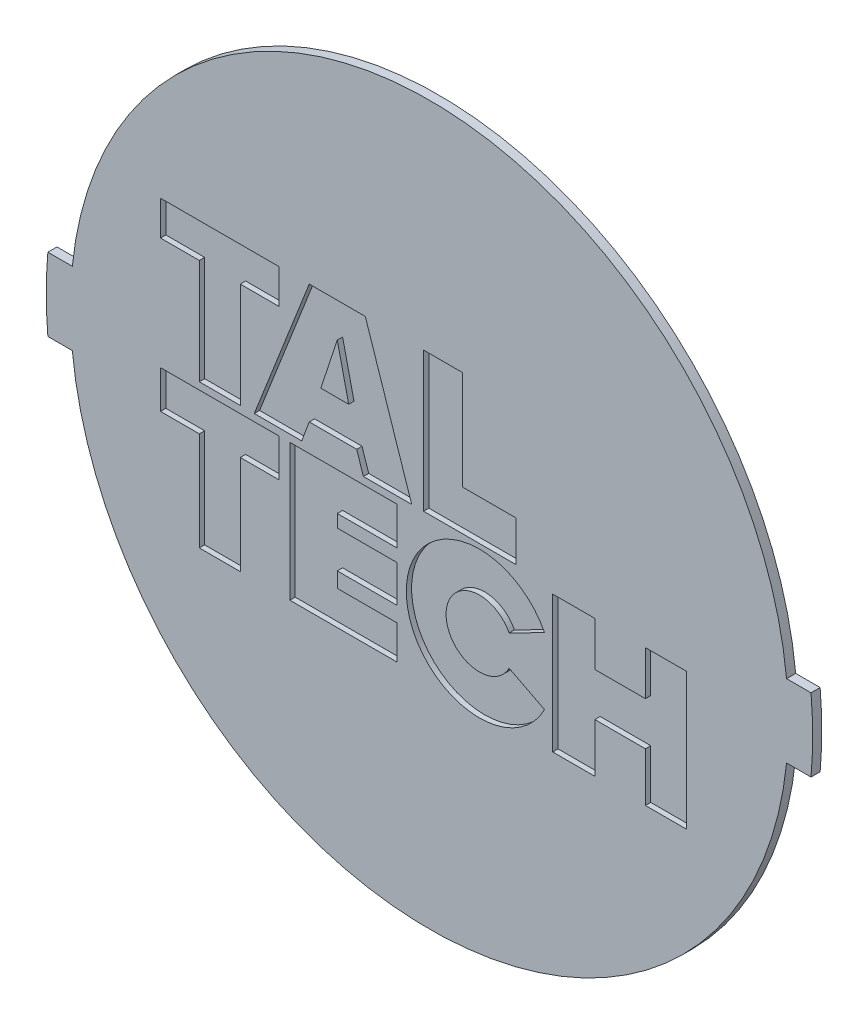
SolidWorks part; units mm, degrees
ref_plane "Alzado" through (0, 0, 0) normal (0, 0, 1) x (1, 0, 0)
ref_plane "Planta" through (0, 0, 0) normal (0, 1, 0) x (1, 0, 0)
ref_plane "Vista lateral" through (0, 0, 0) normal (1, 0, 0) x (0, 0, -1)
sketch "Croquis1" plane through (0, 0, 0) normal (0, 0, 1) x (1, 0, 0)
  circle A0 centre (0, 0) radius 59
  dimension "D1" = 118
extrude "Saliente-Extruir1" add sketch "Croquis1" along normal blind 1.5
sketch "Croquis2" plane through (0, 0, 1.5) normal (0, 0, 1) x (1, 0, 0)
  line L0 (-62.7136, 6) -> (62.7136, 6)
  line L1 (-62.7136, -6) -> (62.7136, -6)
  line L2 (55, 0) -> (-55, 0) construction
  arc A0 (-62.7136, 6) -> (-62.7136, -6) centre (0, 0) ccw
  arc A1 (62.7136, -6) -> (62.7136, 6) centre (0, 0) ccw
  dimension "D1" = 126
  dimension "D2" = 6
  dimension "D3" = 6
extrude "Saliente-Extruir2" add sketch "Croquis2" against normal blind 1.5
scale "Escala1" scale about centroid uniform scaling yes scale factor 0.8
sketch "Croquis7" plane through (0, 0, 1.35) normal (0, 0, 1) x (1, 0, 0)
  line L0 (0.66, 0) -> (-0.66, 0) construction
  line L1 (-35.3595, 18.3529) -> (-19.7701, 18.3529)
  line L2 (-35.3595, 18.3529) -> (-35.3595, 13.8178)
  line L3 (-18.3487, -18.9198) -> (-4.2815, -18.9198)
  line L4 (33.8005, -0.9414) -> (33.8005, -18.9198)
  line L5 (-35.3595, 18.3529) -> (-19.7701, 18.3529)
  line L6 (-35.3595, 18.3529) -> (-35.3595, 13.8178)
  line L7 (-30.2575, 0) -> (-24.8721, 0)
  line L8 (11.4086, 5.3146) -> (11.4086, 0)
  line L9 (-23.0297, 0) -> (-16.794, 0)
  line L10 (-35.3595, 18.3529) -> (-19.7701, 18.3529)
  line L11 (-35.3595, 18.3529) -> (-35.3595, 13.8178)
  line L12 (-35.3595, 13.8178) -> (-30.2575, 13.8178)
  line L13 (-19.7701, 18.3529) -> (-19.7701, 13.8178)
  line L14 (-30.2575, 0) -> (-24.8721, 0)
  line L15 (-30.2575, 0) -> (-30.2575, 13.8178)
  line L17 (-24.8721, 0) -> (-24.8721, 13.8178)
  line L18 (-0.7795, 18.3529) -> (4.3225, 18.3529)
  line L19 (-0.7795, 18.3529) -> (-0.7795, 5.3146)
  line L21 (4.3225, 18.3529) -> (4.3225, 5.3146)
  line L22 (11.4086, 0) -> (-0.7795, 0)
  line L23 (11.4086, 0) -> (11.4086, 5.3146)
  line L24 (11.4086, 5.3146) -> (4.3225, 5.3146)
  line L25 (-0.7795, 0) -> (-0.7795, 5.3146)
  line L26 (-16.794, 0) -> (-15.8019, 2.6573)
  line L27 (-15.8019, 2.6573) -> (-9.5662, 2.6573)
  line L28 (-9.5662, 2.6573) -> (-8.6842, 0)
  line L29 (-8.6842, 0) -> (-2.3384, 0)
  line L30 (-2.3384, 0) -> (-8.4298, 18.3529)
  line L31 (-8.4298, 18.3529) -> (-15.8019, 18.3529)
  line L32 (-15.8019, 18.3529) -> (-23.0297, 0)
  line L33 (-24.8721, 13.8178) -> (-19.7701, 13.8178)
  line L37 (10.4772, -8.2452) -> (15.1331, -5.8593)
  line L38 (-35.3595, -0.9414) -> (-19.7701, -0.9414)
  line L39 (-35.3595, -0.9414) -> (-35.3595, -5.9259)
  line L40 (-35.3595, -5.9259) -> (-30.2575, -5.9259)
  line L41 (-19.7701, -0.9414) -> (-19.7701, -5.9259)
  line L42 (-30.2575, -18.9198) -> (-24.8721, -18.9198)
  line L43 (-30.2575, -18.9198) -> (-30.2575, -5.9259)
  line L45 (-24.8721, -18.9198) -> (-24.8721, -5.9259)
  line L46 (-18.3487, -0.9414) -> (-4.2815, -0.9414)
  line L47 (-18.3487, -0.9414) -> (-18.3487, -18.9198)
  line L48 (-18.3487, -18.9198) -> (-4.2815, -18.9198)
  line L49 (-4.2815, -0.9414) -> (-4.2815, -5.9259)
  line L50 (-12.1159, -12.461) -> (-4.2815, -12.461)
  line L51 (-12.1159, -12.461) -> (-12.1159, -14.4548)
  line L52 (-12.1159, -14.4548) -> (-4.2815, -14.4548)
  line L54 (-12.1159, -5.9259) -> (-4.2815, -5.9259)
  line L55 (-12.1159, -5.9259) -> (-12.1159, -7.5874)
  line L56 (-12.1159, -7.5874) -> (-4.2815, -7.5874)
  line L58 (16.2101, -0.9414) -> (21.7483, -0.9414)
  line L59 (16.2101, -0.9414) -> (16.2101, -18.9198)
  line L60 (16.2101, -18.9198) -> (21.7483, -18.9198)
  line L61 (33.8005, -0.9414) -> (33.8005, -18.9198)
  line L62 (21.7483, -6.7566) -> (28.3942, -6.7566)
  line L63 (21.7483, -6.7566) -> (21.7483, -0.9414)
  line L65 (28.3942, -6.7566) -> (28.3942, -0.9414)
  line L66 (21.7483, -12.461) -> (28.3942, -12.461)
  line L67 (21.7483, -12.461) -> (21.7483, -18.9198)
  line L69 (28.3942, -12.461) -> (28.3942, -18.9198)
  line L70 (15.1331, -5.8593) -> (10.4772, -8.2452)
  line L71 (10.4772, -12.2462) -> (15.1331, -14.6322)
  line L72 (-24.8721, -5.9259) -> (-19.7701, -5.9259)
  line L73 (-4.2815, -7.5874) -> (-4.2815, -12.461)
  line L74 (-4.2815, -14.4548) -> (-4.2815, -18.9198)
  line L75 (28.3942, -0.9414) -> (33.8005, -0.9414)
  line L76 (28.3942, -18.9198) -> (33.8005, -18.9198)
  line L77 (28.3942, -18.9198) -> (33.8005, -18.9198)
  line L78 (16.2101, -18.9198) -> (21.7483, -18.9198)
  line L79 (-35.3595, -0.9414) -> (-35.3595, -5.9259)
  line L80 (-15.8019, 18.3529) -> (-8.4298, 18.3529)
  line L81 (-15.8019, 18.3529) -> (-8.4298, 18.3529)
  line L82 (-23.0297, 0) -> (-16.794, 0)
  line L83 (-8.6842, 0) -> (-2.3384, 0)
  line L84 (-0.7795, 0) -> (11.4086, 0)
  line L85 (-0.7795, 18.3529) -> (4.3225, 18.3529)
  line L86 (-0.7795, 18.3529) -> (4.3225, 18.3529)
  line L87 (-14.2826, 7.2573) -> (-12.1159, 13.8178)
  line L88 (-12.1159, 13.8178) -> (-10.6171, 7.2573)
  line L90 (-113.9494, 23.5401) -> (-113.9494, -26.4599)
  line L91 (-14.2826, 7.2573) -> (-10.6171, 7.2573)
  arc A0 (15.1331, -5.8593) -> (15.1331, -14.6322) centre (6.5735, -10.2457) ccw
  arc A1 (10.4772, -8.2452) -> (10.4772, -12.2462) centre (6.5735, -10.2457) ccw
extrude "Cortar-Extruir1" cut sketch "Croquis7" against normal blind 0.7
